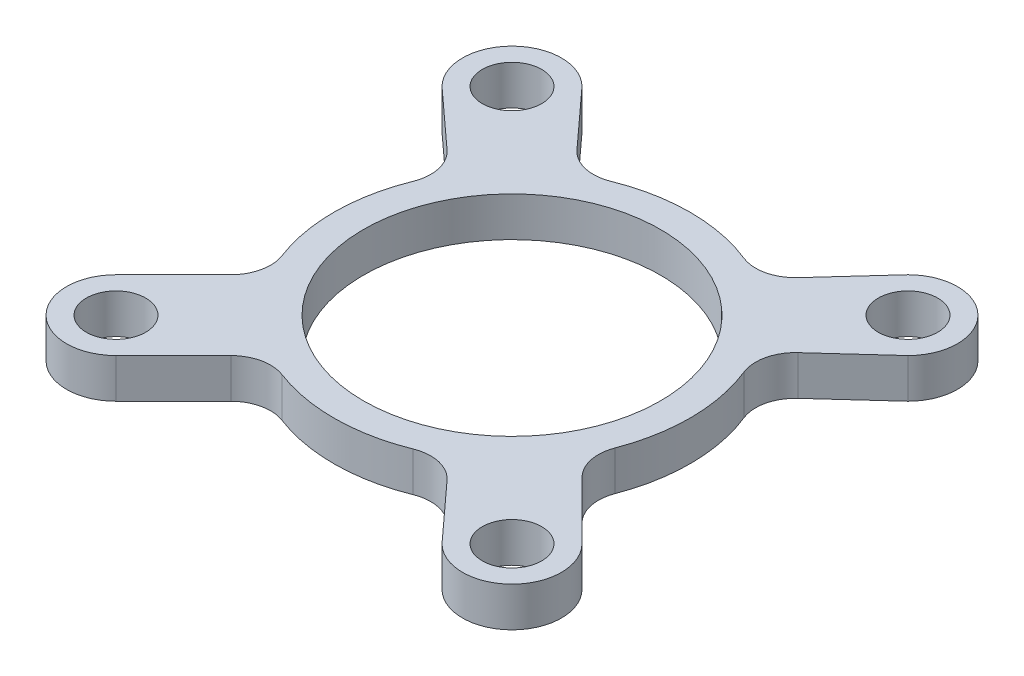
SolidWorks part; units mm, degrees
ref_plane "Front Plane" through (0, 0, 0) normal (0, 0, 1) x (1, 0, 0)
ref_plane "Top Plane" through (0, 0, 0) normal (0, 1, 0) x (1, 0, 0)
ref_plane "Right Plane" through (0, 0, 0) normal (1, 0, 0) x (0, 0, -1)
sketch "Sketch1" plane through (0, 0, 0) normal (0, 1, 0) x (1, 0, 0)
  line L0 (-10, 10) -> (10, -10) construction
  line L1 (-10, -10) -> (10, 10) construction
  line L2 (0, 0) -> (-16.2687, 0) construction
  line L3 (-11.7678, -8.2322) -> (-8.2322, -11.7678) construction
  line L4 (-11.7678, -8.2322) -> (-7.8813, -4.3457)
  line L5 (-8.2322, -11.7678) -> (-4.3457, -7.8813)
  line L6 (11.7678, 8.2322) -> (7.7529, 4.5709)
  line L7 (8.2322, 11.7678) -> (4.5709, 7.7529)
  line L8 (8.2322, -11.7678) -> (11.7678, -8.2322) construction
  line L9 (11.7678, -8.2322) -> (7.8813, -4.3457)
  line L10 (8.2322, -11.7678) -> (4.5709, -7.7529)
  line L11 (-11.7678, 8.2322) -> (-8.2322, 11.7678) construction
  line L12 (-11.7678, 8.2322) -> (-7.7529, 4.5709)
  line L13 (-8.2322, 11.7678) -> (-4.5709, 7.7529)
  circle A0 centre (0, 0) radius 7.5
  arc A1 (-11.7678, -8.2322) -> (-8.2322, -11.7678) centre (-10, -10) ccw
  arc A2 (8.2322, 11.7678) -> (11.7678, 8.2322) centre (10, 10) cw
  arc A3 (8.2322, -11.7678) -> (11.7678, -8.2322) centre (10, -10) ccw
  arc A4 (-11.7678, 8.2322) -> (-8.2322, 11.7678) centre (-10, 10) cw
  circle A9 centre (-10, -10) radius 1.5
  circle A10 centre (10, -10) radius 1.5
  circle A11 centre (10, 10) radius 1.5
  circle A12 centre (-10, 10) radius 1.5
  arc A13 (4.5709, 7.7529) -> (-4.5709, 7.7529) centre (0, 0) ccw
  arc A14 (7.8813, -4.3457) -> (7.7529, 4.5709) centre (0, 0) ccw
  arc A15 (-4.3457, -7.8813) -> (4.5709, -7.7529) centre (0, 0) ccw
  arc A16 (-7.7529, 4.5709) -> (-7.8813, -4.3457) centre (0, 0) ccw
  point P6 (0, 0)
  point P9 (0, 0)
  dimension "D1" = 15
  dimension "D2" = 5
  dimension "D5" = 5
  dimension "D7" = 3
  dimension "D8" = 18
  dimension "D3" = 10
  dimension "D4" = 45
extrude "Boss-Extrude1" add sketch "Sketch1" along normal blind 2
fillet "Fillet1" radius 2 8 edges at (7.8813, 1, 4.3457) (7.7529, 1, -4.5709) (4.5709, 1, 7.7529) (-4.3457, 1, 7.8813) (-7.8813, 1, 4.3457) (-7.7529, 1, -4.5709) (4.5709, 1, -7.7529) (-4.5709, 1, -7.7529)
